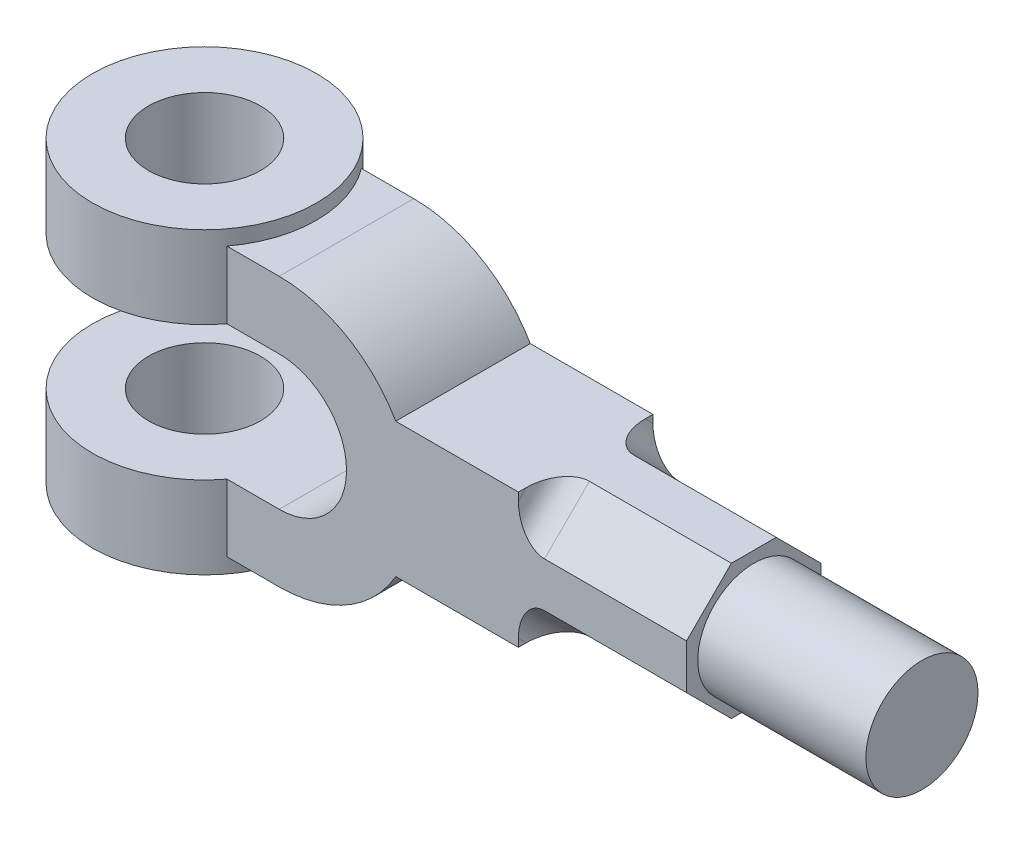
SolidWorks part; units mm, degrees
ref_plane "Front Plane" through (0, 0, 0) normal (0, 0, 1) x (1, 0, 0)
ref_plane "Top Plane" through (0, 0, 0) normal (0, 1, 0) x (1, 0, 0)
ref_plane "Right Plane" through (0, 0, 0) normal (1, 0, 0) x (0, 0, -1)
sketch "Sketch1" plane through (0, 0, 0) normal (0, 0, 1) x (1, 0, 0)
  line L1 (31.1769, 18) -> (109, 18)
  line L3 (31.1769, -18) -> (109, -18)
  line L4 (109, 18) -> (109, -18)
  line L5 (0, 36) -> (-38, 36)
  line L7 (0, 18) -> (-38, 18)
  line L8 (-38, 36) -> (-38, 18)
  line L9 (0, -18) -> (-38, -18)
  line L11 (0, -36) -> (-38, -36)
  line L12 (-38, -18) -> (-38, -36)
  arc A0 (0, -36) -> (31.1769, -18) centre (0, 0) ccw
  arc A1 (0, -18) -> (0, 18) centre (0, 0) ccw
  arc A2 (31.1769, 18) -> (0, 36) centre (0, 0) ccw
  dimension "D1" = 72
  dimension "D2" = 36
  dimension "D3" = 36
  dimension "D4" = 109
  dimension "D5" = 147
  dimension "D6" = 147
extrude "Boss-Extrude1" add sketch "Sketch1" along normal mid plane 36
sketch "Sketch2" plane through (0, 18, 0) normal (0, -1, 0) x (1, 0, 0)
  line L0 (-38, 18) -> (-38, -18) construction
  circle A0 centre (-38, 0) radius 30
  dimension "D1" = 60
extrude "Boss-Extrude2" add sketch "Sketch2" against normal blind 22
sketch "Sketch3" plane through (0, -18, 0) normal (0, 1, 0) x (1, 0, 0)
  circle A0 centre (-38, 0) radius 30
extrude "Boss-Extrude3" add sketch "Sketch3" against normal blind 22
sketch "Sketch4" plane through (0, 40, 0) normal (0, 1, 0) x (1, 0, 0)
  circle A0 centre (-38, 0) radius 15
  dimension "D1" = 30
extrude "Cut-Extrude1" cut sketch "Sketch4" against normal through all
sketch "Sketch5" plane through (109, 0, 0) normal (1, 0, 0) x (0, 0, -1)
  line L0 (6, 18) -> (18, 6)
  line L1 (-18, 18) -> (18, 18) construction
  line L2 (18, -18) -> (18, 18) construction
  line L3 (18, 6) -> (18, 18)
  line L4 (18, 18) -> (6, 18)
  line L5 (18, -18) -> (18, -6)
  line L6 (18, -6) -> (6, -18)
  line L7 (6, -18) -> (18, -18)
  line L8 (-18, -18) -> (-6, -18)
  line L9 (-6, -18) -> (-18, -6)
  line L10 (-18, -6) -> (-18, -18)
  line L11 (-18, 18) -> (-18, 6)
  line L12 (-18, 6) -> (-6, 18)
  line L13 (-6, 18) -> (-18, 18)
  point P6 (0, 0)
  point P22 (0, 0)
  dimension "D1" = 12
  dimension "D2" = 12
  dimension "D3" = 4
extrude "Cut-Extrude2" cut sketch "Sketch5" against normal blind 45
fillet "Fillet1" radius 7 4 edges at (64, -12, 12) (64, -12, -12) (64, 12, -12) (64, 12, 12)
sketch "Sketch6" plane through (109, 0, 0) normal (1, 0, 0) x (0, 0, -1)
  circle A0 centre (0, 0) radius 15
  dimension "D1" = 30
extrude "Boss-Extrude4" add sketch "Sketch6" along normal blind 45
